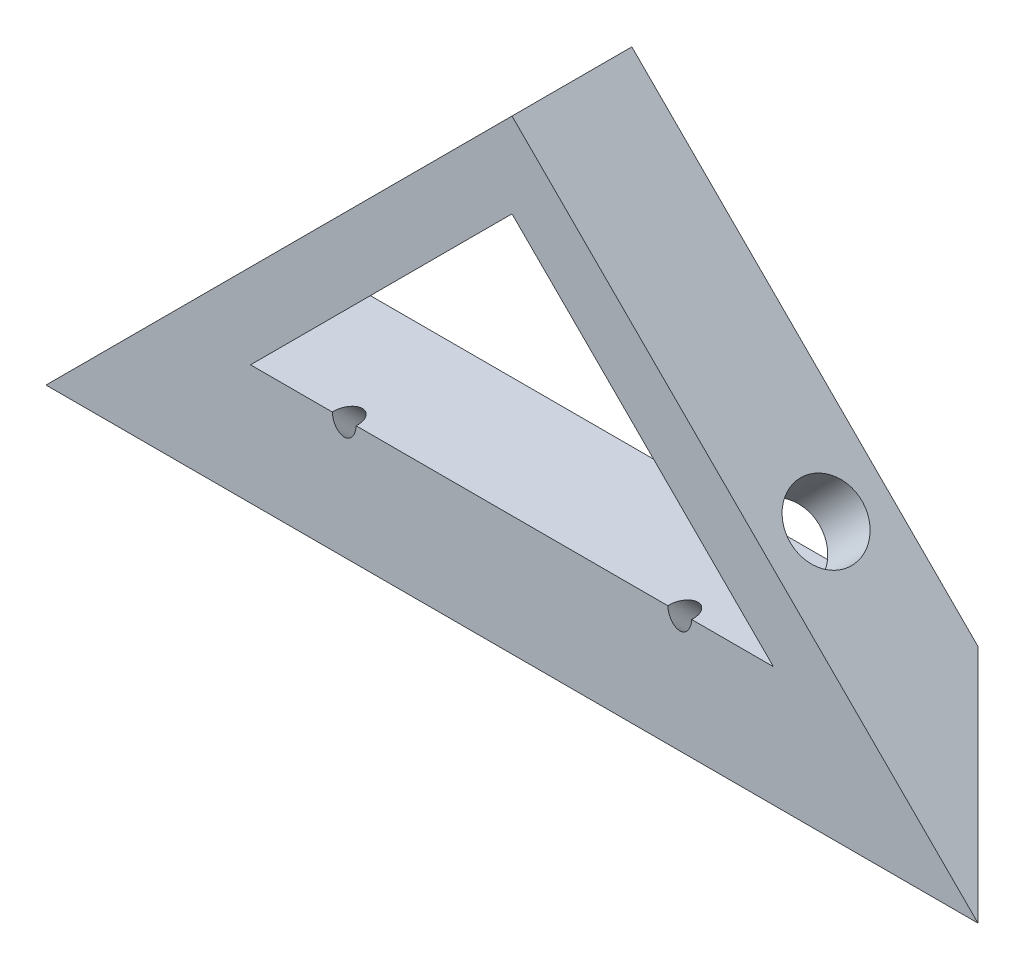
SolidWorks part; units mm, degrees
ref_plane "Front Plane" through (0, 0, 0) normal (0, 0, 1) x (1, 0, 0)
ref_plane "Top Plane" through (0, 0, 0) normal (0, 1, 0) x (1, 0, 0)
ref_plane "Right Plane" through (0, 0, 0) normal (1, 0, 0) x (0, 0, -1)
sketch "Sketch4" plane through (0, 0, 0) normal (0, 0, 1) x (1, 0, 0)
  line L0 (0, 28.8909) -> (-38.8909, -10)
  line L1 (-38.8909, -10) -> (38.8909, -10)
  line L2 (38.8909, -10) -> (0, 28.8909)
  line L3 (26.8198, -5) -> (0, 21.8198)
  line L4 (0, 21.8198) -> (-26.8198, -5)
  line L5 (-26.8198, -5) -> (26.8198, -5) construction
  line L6 (-14.7487, 0) -> (14.7487, 0)
  line L7 (14.7487, 0) -> (0, 14.7487) construction
  line L8 (0, 14.7487) -> (-14.7487, 0) construction
  line L9 (-14.7487, 0) -> (-21.8198, 0)
  line L10 (14.7487, 0) -> (21.8198, 0)
  point P10 (21.8198, 0)
  point P13 (21.751, 0)
  point P14 (-21.8198, 0)
  dimension "D1" = 90
  dimension "D2" = 45
  dimension "D3" = 55
  dimension "D4" = 10
  dimension "D5" = 0
  dimension "D6" = 5
  dimension "D7" = 5
sketch "Sketch6" plane through (0, 0, 0) normal (1, 0, 0) x (0, 0, -1)
  line L0 (-10, -10) -> (0, 0)
  line L1 (0, 0) -> (0, -10)
  line L2 (0, -10) -> (-10, -10)
  dimension "D1" = 10
  dimension "D2" = 10
  dimension "D3" = 45
  dimension "D4" = 10
extrude "Boss-Extrude4" add sketch "Sketch4" along normal blind 10
extrude "Cut-Extrude2" cut sketch "Sketch6" against normal through all both and the other way through all
sketch "Sketch7" plane through (-14.4454, 14.4454, 0) normal (-0.7071, 0.7071, 0) x (0, 0, 1)
  line L0 (10, 20.4289) -> (10, -34.5711) construction
  line L1 (10, 20.4289) -> (0, 20.4289) construction
  circle A0 centre (5, -9.5711) radius 3
  dimension "D1" = 6
  dimension "D2" = 5
  dimension "D3" = 30
extrude "Cut-Extrude3" cut sketch "Sketch7" against normal up to next
sketch "Sketch8" plane through (14.4454, 14.4454, 0) normal (0.7071, 0.7071, 0) x (0, 0, -1)
  line L0 (-10, -34.5711) -> (-10, 20.4289) construction
  line L1 (-10, 20.4289) -> (0, 20.4289) construction
  circle A0 centre (-5, -9.5711) radius 3
  dimension "D1" = 6
  dimension "D2" = 5
  dimension "D3" = 30
extrude "Cut-Extrude4" cut sketch "Sketch8" against normal up to next
sketch "Sketch9" plane through (0, 0, 0) normal (0, -0.7071, -0.7071) x (1, 0, 0)
  line L0 (0, 0) -> (0, -15.8975) construction
  circle A0 centre (-14, 7) radius 1
  circle A1 centre (14, 7) radius 1
  dimension "D1" = 2
  dimension "D2" = 14
  dimension "D3" = 7
extrude "Cut-Extrude5" cut sketch "Sketch9" against normal up to next
